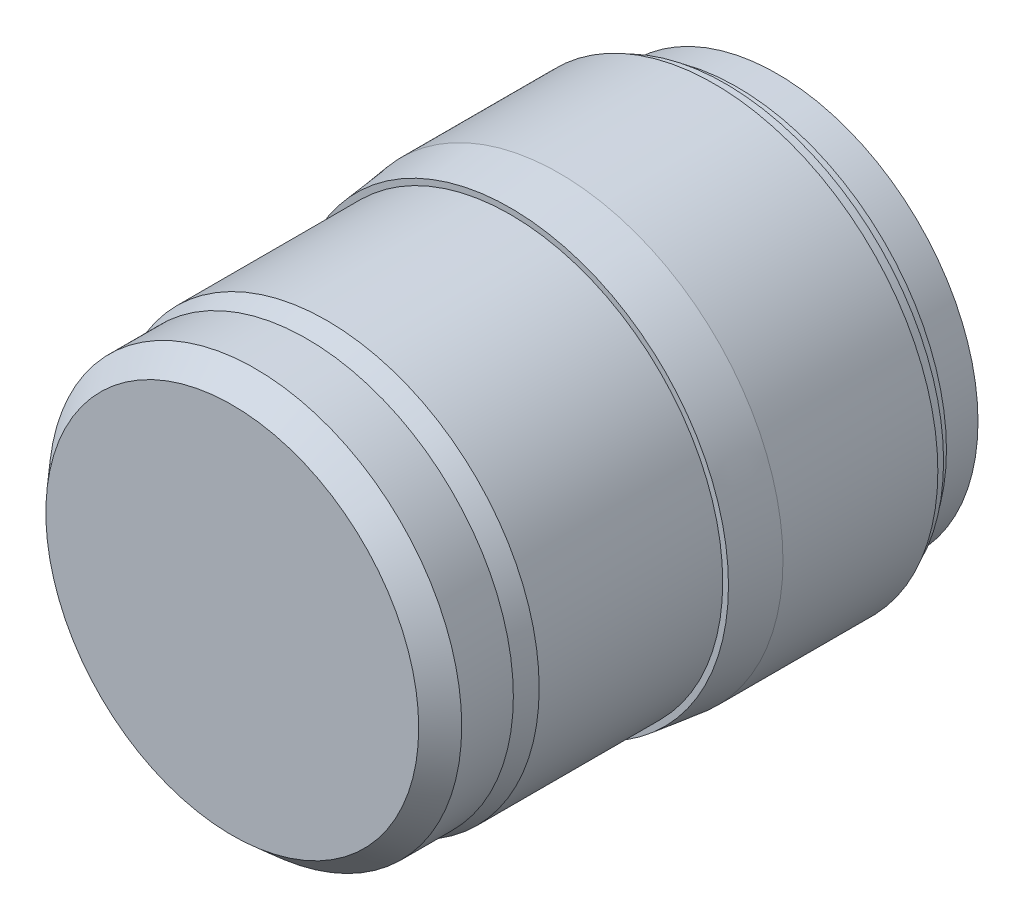
SolidWorks part; units mm, degrees
ref_plane "Спереди" through (0, 0, 0) normal (0, 0, 1) x (1, 0, 0)
ref_plane "Сверху" through (0, 0, 0) normal (0, 1, 0) x (1, 0, 0)
ref_plane "Справа" through (0, 0, 0) normal (1, 0, 0) x (0, 0, -1)
sketch "Эскиз1" plane through (0, 0, 0) normal (0, 1, 0) x (1, 0, 0)
  line L0 (0, 95) -> (35, 95)
  line L1 (35, 95) -> (35, 88)
  line L2 (35, 88) -> (36.5, 88)
  line L3 (36.5, 88) -> (36.5, 86.001)
  line L4 (39, 57.001) -> (38, 48.501)
  line L5 (38, 48.501) -> (37, 48.501)
  line L6 (37, 48.501) -> (37, 16.501)
  line L7 (37, 16.501) -> (36, 13)
  line L8 (36, 13) -> (36, 4)
  line L9 (36, 4) -> (32.5, 0)
  line L10 (32.5, 0) -> (0, 0)
  line L11 (0, 0) -> (0, 95)
  line L12 (36.5, 86.001) -> (38, 86.001)
  line L13 (38, 86.001) -> (38, 84.001)
  line L14 (38, 84.001) -> (39, 84.001)
  line L15 (39, 84.001) -> (39, 57.001)
  dimension "D2" = 7
  dimension "D3" = 1.999
  dimension "D4" = 2
  dimension "D5" = 27
  dimension "D6" = 8.5
  dimension "D7" = 32
  dimension "D8" = 9
  dimension "D9" = 4
  dimension "D10" = 32.5
  dimension "D11" = 36
  dimension "D12" = 37
  dimension "D13" = 39
  dimension "D14" = 38
  dimension "D15" = 36.5
  dimension "D16" = 35
  dimension "D17" = 95
  dimension "D18" = 1
revolve "Повернуть1" add sketch "Эскиз1" angle 360 about L11
